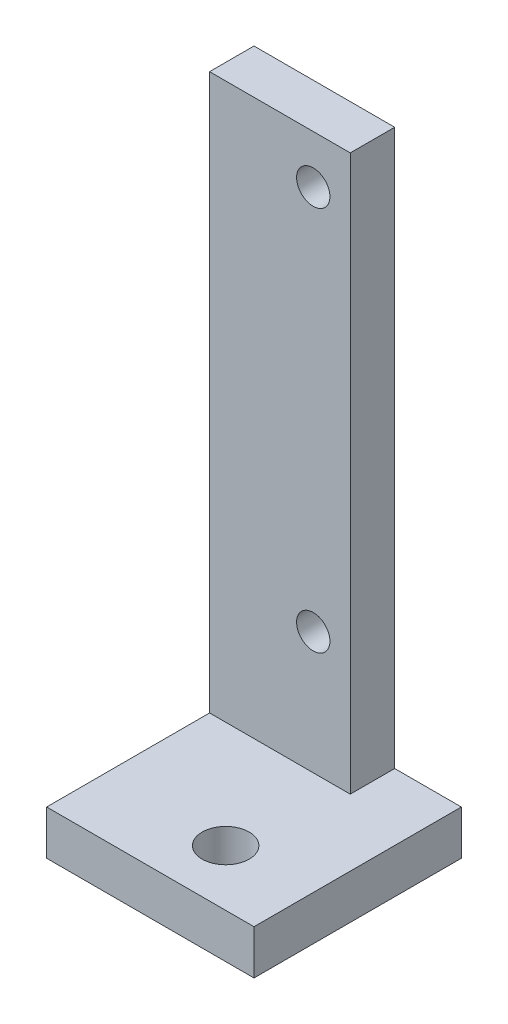
SolidWorks part; units mm, degrees
ref_plane "Front Plane" through (0, 0, 0) normal (0, 0, 1) x (1, 0, 0)
ref_plane "Top Plane" through (0, 0, 0) normal (0, 1, 0) x (1, 0, 0)
ref_plane "Right Plane" through (0, 0, 0) normal (1, 0, 0) x (0, 0, -1)
sketch "Sketch1" plane through (0, 0, 0) normal (0, 0, 1) x (1, 0, 0)
  line L0 (55, 0) -> (-55, 0) construction
  line L1 (-5, 32.5) -> (5, 32.5)
  line L2 (-5, 32.5) -> (-5, -32.5)
  line L3 (-5, -32.5) -> (5, -32.5)
  line L4 (5, 32.5) -> (5, -32.5)
  line L5 (-5, 32.5) -> (5, -32.5) construction
  line L6 (-5, -32.5) -> (5, 32.5) construction
  line L8 (-5, -32.5) -> (5, -32.5)
  line L9 (-5, -32.5) -> (-5, -42.5)
  line L10 (-5, -42.5) -> (5, -42.5)
  line L11 (5, -32.5) -> (5, -42.5)
  circle A0 centre (0, 26) radius 2.25
  circle A1 centre (0, -26) radius 2.25
  point P0 (0, 0)
  dimension "D2" = 4.5
  dimension "D1" = 65
  dimension "D3" = 26
  dimension "D4" = 10
  dimension "D5" = 10
extrude "Boss-Extrude1" add sketch "Sketch1" along normal blind 6 contours L11 L3 L9 L10 | L4 L1 L2 L3 A0 A1
sketch "Sketch2" plane through (0, -42.5, 0) normal (0, -1, 0) x (1, 0, 0)
  line L0 (-14, 0) -> (-14, 28)
  line L1 (-14, 0) -> (14, 0)
  line L2 (0, 0) -> (0, 28)
  line L3 (-14, 28) -> (14, 28)
  line L4 (14, 0) -> (14, 28)
  circle A0 centre (2.6, 20.4299) radius 3.175
  line M2 (-5, 0) -> (5, 0)
  line M3 (5, 0) -> (5, 6)
  line M4 (5, 6) -> (-5, 6)
  line M5 (-5, 6) -> (-5, 0)
  dimension "D2" = 6.35
  dimension "D1" = 2.6
  dimension "D3" = 28
  dimension "D4" = 28
extrude "Boss-Extrude2" add sketch "Sketch2" along normal blind 6 separate body contours L3 L0 L1 L2 M5 M4 | L2 M2 M4 M5 | L2 L1 M3 M4 | L1 L4 L3 L2 A0 M4 M3
sketch "Sketch3" plane through (-5, 0, 0) normal (-1, 0, 0) x (0, 0, 1)
  line L0 (0, -42.5) -> (28, -42.5) construction
  line L1 (0, 32.5) -> (6, 32.5)
  line L2 (0, 32.5) -> (0, -42.5)
  line L3 (0, -42.5) -> (6, -42.5)
  line L4 (6, 32.5) -> (6, -42.5)
extrude "Boss-Extrude3" add sketch "Sketch3" along normal up to surface (9 mm away) up to face at (-14, -45.5, 14)
